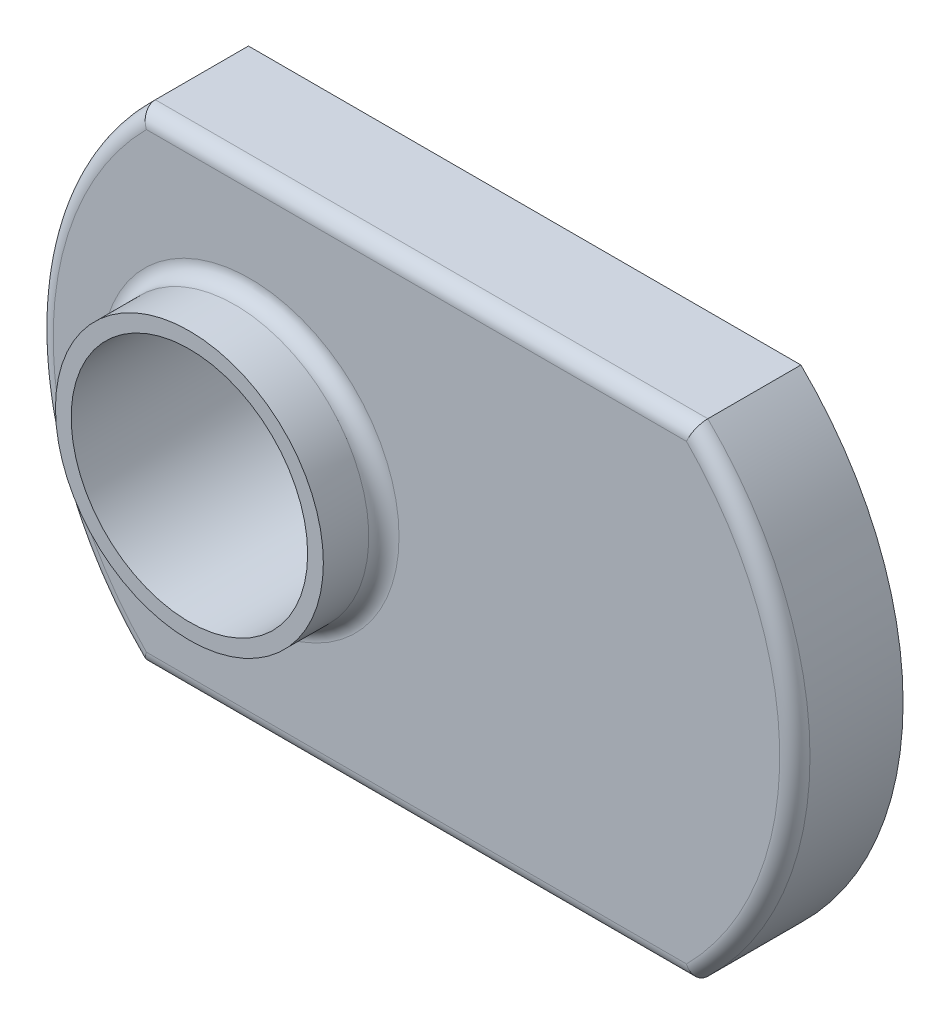
SolidWorks part; units mm, degrees
ref_plane "Front"
ref_plane "Top" through (0, 0, 0) normal (0, 1, 0) x (1, 0, 0)
ref_plane "Right" through (0, 0, 0) normal (1, 0, 0) x (0, 0, -1)
sketch "Sketch1" plane through (0, 0, 0) normal (0, 0, 1) x (1, 0, 0)
  line L1 (0, 0) -> (25.4, 0)
  line L2 (0, 0) -> (0, 16.2052)
  line L3 (0, 16.2052) -> (25.4, 16.2052)
  line L4 (25.4, 0) -> (25.4, 16.2052)
  dimension "D1" = 16.2052
  dimension "D2" = 25.4
extrude "Base-Extrude" add sketch "Sketch1" against normal blind 3.6322
sketch "Sketch2" plane through (0, 0, 0) normal (0, 0, 1) x (1, 0, 0)
  line L0 (0, 8.1026) -> (25.4, 8.1026) construction
  line L1 (0, 16.2052) -> (0, 0) construction
  line L2 (25.4, 0) -> (25.4, 16.2052) construction
  circle A0 centre (7.112, 8.1026) radius 4.4958
  dimension "D1" = 8.9916
  dimension "D2" = 7.112
extrude "Boss-Extrude1" add sketch "Sketch2" along normal blind 2.032
hole_wizard "5/16-18 Tapped Hole1" positions "3DSketch1" profile "Sketch3" tap size "5/16-18" standard "Ansi Inch"
sketch3d "3DSketch1"
  line L0 (7.112, 8.1026, 2.032) -> (7.112, 8.1026, 0) construction
  point P0 (7.112, 8.1026, 2.032)
  point P3 (7.112, 8.1026, 2.032)
sketch "Sketch3" plane through (7.112, 8.1026, 2.032) normal (1, 0, 0) x (0, -1, 0)
  line L0 (0, 0) -> (0, 5.6642)
  line L1 (0, 5.6642) -> (3.2639, 5.6642)
  line L3 (3.2639, 5.6642) -> (3.2639, 15.875)
  line L4 (3.2639, 15.875) -> (3.9687, 15.875)
  line L5 (3.9687, 15.875) -> (3.9687, 0)
  line L7 (3.9687, 0) -> (0, 0)
  line L11 (0, -6.35) -> (0, 107.95) construction
  dimension "Thru Tap Drill Dia." = 6.5278
  dimension "Thru Tap Drill Depth" = 5.6642
  dimension "Thread Dia." = 7.9375
  dimension "Thread Depth" = 15.875
sketch "Sketch4" plane through (0, 0, 0) normal (0, 0, 1) x (1, 0, 0)
  line L0 (25.4, 16.2052) -> (0, 16.2052) construction
  line L1 (0, 0) -> (25.4, 0) construction
  line L2 (25.4, 0) -> (25.4, 16.2052) construction
  arc A0 (21.971, 16.2052) -> (21.971, 0) centre (14.1124, 8.1026) cw
  dimension "D1" = 3.429
extrude "Cut-Extrude1" cut sketch "Sketch4" against normal through all and the other way through all
sketch "Sketch6" plane through (0, 0, 0) normal (0, 0, 1) x (1, 0, 0)
  line L0 (21.971, 16.2052) -> (0, 16.2052) construction
  line L1 (0, 0) -> (21.971, 0) construction
  line L2 (0, 16.2052) -> (0, 0) construction
  arc A0 (3.429, 16.2052) -> (3.429, 0) centre (11.2876, 8.1026) ccw
  dimension "D1" = 3.429
extrude "Cut-Extrude2" cut sketch "Sketch6" against normal through all and the other way through all flip side to cut
fillet "Fillet1" radius 0.508
